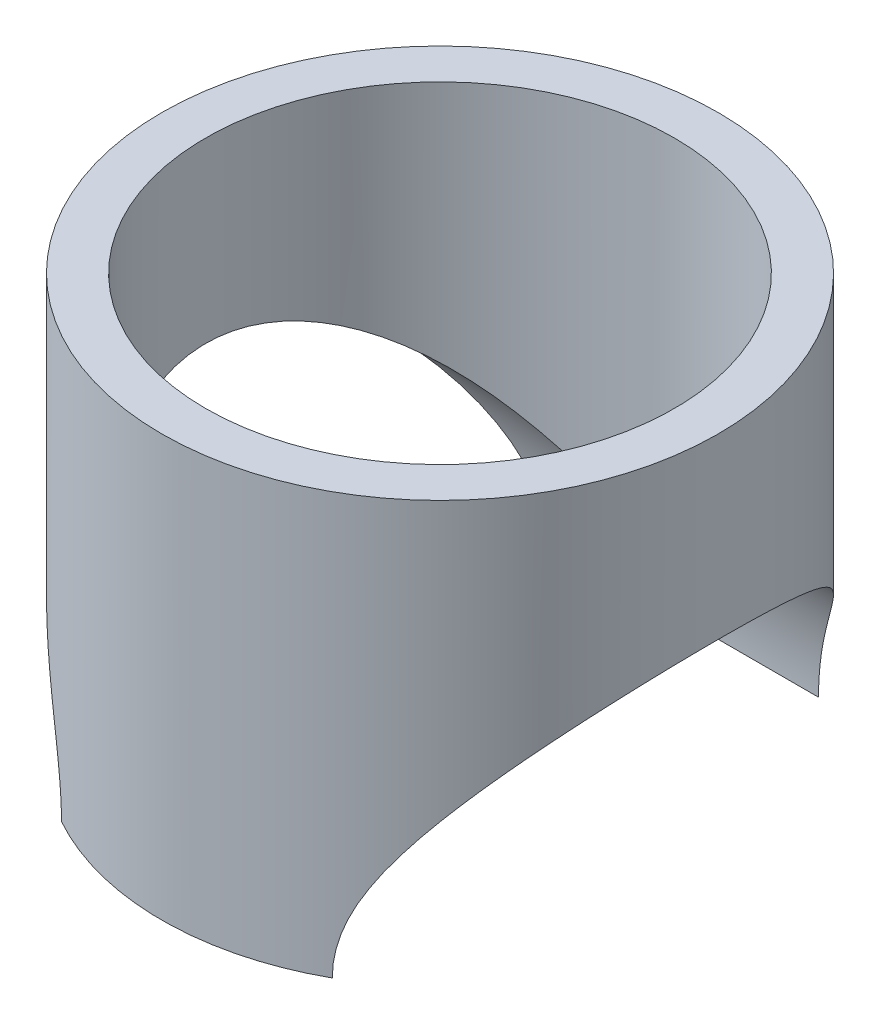
SolidWorks part; units mm, degrees
material "6061-O (SS)"
ref_plane "Front Plane" through (0, 0, 0) normal (0, 0, 1) x (1, 0, 0)
ref_plane "Top Plane" through (0, 0, 0) normal (0, 1, 0) x (1, 0, 0)
ref_plane "Right Plane" through (0, 0, 0) normal (1, 0, 0) x (0, 0, -1)
sketch "Sketch1" plane through (0, 0, 0) normal (0, 1, 0) x (1, 0, 0)
  circle A0 centre (0, 0) radius 24.13
  circle A1 centre (0, 0) radius 20.32
  dimension "D1" = 48.26
  dimension "D2" = 40.64
extrude "Boss-Extrude1" add sketch "Sketch1" along normal mid plane 36.5125
hole_wizard "3/32 (1.66) Dowel Hole1" positions "Sketch5" profile "Sketch6" hole size "3/32" standard "ANSI Inch"
sketch "Sketch5" plane through (0, 0, 0) normal (1, 0, 0) x (0, 0, -1)
  line L0 (-24.13, -18.2562) -> (24.13, -18.2562) construction
  point P0 (0, -18.2562)
  dimension "D1" = 0
sketch "Sketch6" plane through (0, -18.2562, 0) normal (0, 1, 0) x (0, 0, -1)
  line L0 (0, 0) -> (0, 24.13)
  line L1 (0, 24.13) -> (21.082, 24.13)
  line L2 (21.082, 24.13) -> (21.082, 0)
  line L5 (21.082, 0) -> (0, 0)
  line L11 (0, -6.35) -> (0, 107.95) construction
  dimension "Thru Hole Dia." = 42.164
  dimension "Thru Hole Depth" = 24.13
mirror "Mirror1" about plane through (0, 0, 0) normal (1, 0, 0) of "3/32 (1.66) Dowel Hole1"
